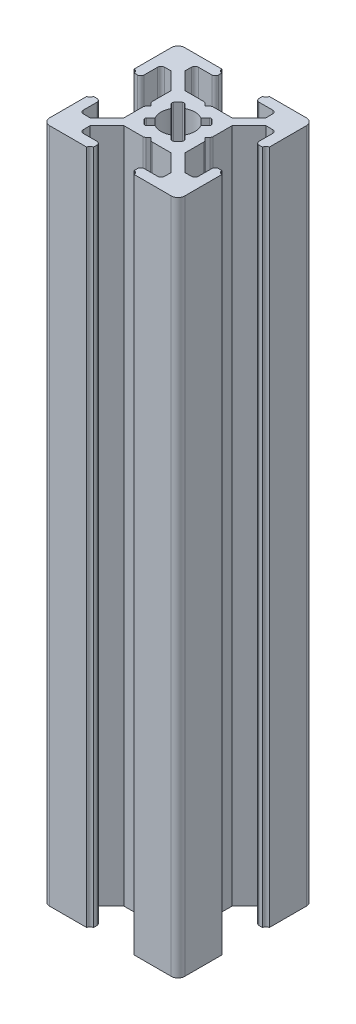
SolidWorks part; units mm, degrees
ref_plane "Front Plane" through (0, 0, 0) normal (0, 0, 1) x (1, 0, 0)
ref_plane "Top Plane" through (0, 0, 0) normal (0, 1, 0) x (1, 0, 0)
ref_plane "Right Plane" through (0, 0, 0) normal (1, 0, 0) x (0, 0, -1)
sketch "Sketch3" plane through (0, 0, 0) normal (0, 1, 0) x (1, 0, 0)
  line L0 (7, 20) -> (7, 18.5)
  line L1 (0, 0) -> (20, 0)
  line L2 (0, 0) -> (0, 20)
  line L3 (0, 20) -> (20, 20)
  line L4 (20, 0) -> (20, 20)
  line L5 (7, 18.5) -> (4, 18.5)
  line L6 (4, 18.5) -> (4, 17)
  line L7 (4, 17) -> (6.5, 14.5)
  line L8 (6.5, 14.5) -> (13.5, 14.5)
  line L9 (13.5, 14.5) -> (16, 17)
  line L10 (16, 17) -> (16, 18.5)
  line L11 (16, 18.5) -> (13, 18.5)
  line L12 (13, 18.5) -> (13, 20)
  line L13 (13, 20) -> (7, 20)
  line L14 (9.5, 14.5) -> (10, 14)
  line L15 (10, 14) -> (10.5, 14.5)
  line L16 (10.5, 14.5) -> (9.5, 14.5)
  line L17 (13, 19.5) -> (13, 20)
  line L18 (13.5, 20) -> (13, 20)
  line L19 (7, 19.5) -> (7, 20)
  line L20 (6.5, 20) -> (7, 20)
  line L21 (0, 13) -> (1.5, 13)
  line L22 (1.5, 13) -> (1.5, 16)
  line L23 (1.5, 16) -> (3, 16)
  line L24 (3, 16) -> (5.5, 13.5)
  line L25 (5.5, 13.5) -> (5.5, 6.5)
  line L26 (5.5, 6.5) -> (3, 4)
  line L27 (3, 4) -> (1.5, 4)
  line L28 (1.5, 4) -> (1.5, 7)
  line L29 (1.5, 7) -> (0, 7)
  line L30 (0, 7) -> (0, 13)
  line L31 (5.5, 10.5) -> (5.5, 9.5)
  line L32 (5.5, 9.5) -> (6, 10)
  line L33 (6, 10) -> (5.5, 10.5)
  line L34 (0.5, 13) -> (0, 13)
  line L35 (0, 13.5) -> (0, 13)
  line L36 (0, 6.5) -> (0, 7)
  line L37 (0.5, 7) -> (0, 7)
  line L38 (10, 20) -> (10, 0) construction
  line L39 (20, 10) -> (0, 10) construction
  line L40 (10, 6) -> (10.5, 5.5)
  line L41 (9.5, 5.5) -> (10, 6)
  line L42 (10.5, 5.5) -> (9.5, 5.5)
  line L43 (13.5, 0) -> (13, 0)
  line L44 (13, 0.5) -> (13, 0)
  line L45 (6.5, 0) -> (7, 0)
  line L46 (7, 0.5) -> (7, 0)
  line L47 (13, 1.5) -> (13, 0)
  line L48 (16, 1.5) -> (13, 1.5)
  line L49 (16, 3) -> (16, 1.5)
  line L50 (13.5, 5.5) -> (16, 3)
  line L51 (6.5, 5.5) -> (13.5, 5.5)
  line L52 (4, 3) -> (6.5, 5.5)
  line L53 (4, 1.5) -> (4, 3)
  line L54 (7, 1.5) -> (4, 1.5)
  line L55 (7, 0) -> (7, 1.5)
  line L56 (13, 0) -> (7, 0)
  line L57 (14.5, 9.5) -> (14, 10)
  line L58 (14.5, 10.5) -> (14.5, 9.5)
  line L59 (14, 10) -> (14.5, 10.5)
  line L60 (19.5, 7) -> (20, 7)
  line L61 (20, 6.5) -> (20, 7)
  line L62 (20, 13.5) -> (20, 13)
  line L63 (19.5, 13) -> (20, 13)
  line L64 (18.5, 7) -> (20, 7)
  line L65 (18.5, 4) -> (18.5, 7)
  line L66 (17, 4) -> (18.5, 4)
  line L67 (14.5, 6.5) -> (17, 4)
  line L68 (14.5, 13.5) -> (14.5, 6.5)
  line L69 (17, 16) -> (14.5, 13.5)
  line L70 (18.5, 16) -> (17, 16)
  line L71 (18.5, 13) -> (18.5, 16)
  line L72 (20, 13) -> (18.5, 13)
  line L73 (20, 7) -> (20, 13)
  arc A0 (13.5, 20) -> (13, 19.5) centre (13, 20) cw
  arc A1 (6.5, 20) -> (7, 19.5) centre (7, 20) ccw
  arc A2 (0.5, 13) -> (0, 13.5) centre (0, 13) ccw
  arc A3 (0.5, 7) -> (0, 6.5) centre (0, 7) cw
  arc A4 (13.5, 0) -> (13, 0.5) centre (13, 0) ccw
  arc A5 (6.5, 0) -> (7, 0.5) centre (7, 0) cw
  arc A6 (19.5, 7) -> (20, 6.5) centre (20, 7) ccw
  arc A7 (19.5, 13) -> (20, 13.5) centre (20, 13) cw
  point P7 (10, 14.5)
  point P16 (10, 20)
  point P26 (5.5, 10)
  point P35 (0, 10)
  dimension "D16" = 0.5
  dimension "D17" = 0.5
  dimension "D28" = 0.5
  dimension "D29" = 0.5
  dimension "D1" = 20
  dimension "D2" = 20
  dimension "D3" = 7
  dimension "D4" = 7
  dimension "D5" = 1.5
  dimension "D6" = 1.5
  dimension "D7" = 3
  dimension "D8" = 3
  dimension "D9" = 1.5
  dimension "D10" = 1.5
  dimension "D11" = 7
  dimension "D12" = 5.5
  dimension "D13" = 0.5
  dimension "D14" = 0.5
  dimension "D15" = 0.5
  dimension "D18" = 7
  dimension "D19" = 7
  dimension "D20" = 1.5
  dimension "D21" = 1.5
  dimension "D22" = 3
  dimension "D23" = 7
  dimension "D24" = 5.5
  dimension "D25" = 0.5
  dimension "D26" = 0.5
  dimension "D27" = 0.5
extrude "Boss-Extrude1" add sketch "Sketch3" along normal blind 100 contours L72 A7 L4 L3 A0 L12 L11 L10 L9 L8 L15 L14 L7 L6 L5 L0 A1 L2 A2 L21 L22 L23 L24 L25 L33 L32 L26 L27 L28 L29 A3 L1 A5 L55 L54 L53 L52 L51 L41 L40 L50 L49 L48 L47 A4
fillet "Fillet1" radius 1 4 edges at (0, 50, 0) (20, 50, 0) (20, 50, -20) (0, 50, -20)
sketch "Sketch4" plane through (0, 100, 0) normal (0, 1, 0) x (1, 0, 0)
  line L0 (13.5, 14.5) -> (5.5, 6.5) construction
  line L1 (14.5, 13.5) -> (6.5, 5.5) construction
  line L2 (10.5, 14.5) -> (14.5, 10.5) construction
  line L3 (12, 13) -> (13, 12)
  line L4 (13, 12) -> (8, 7)
  line L5 (8, 7) -> (7, 8)
  line L6 (7, 8) -> (12, 13)
  line L7 (13.5, 14.5) -> (16, 17) construction
  line L8 (17, 16) -> (14.5, 13.5) construction
  line L9 (5.5, 9.5) -> (9.5, 5.5) construction
  line L10 (5.5, 10.5) -> (9.5, 14.5) construction
  line L11 (14.5, 9.5) -> (10.5, 5.5) construction
  line L12 (6.5, 14.5) -> (14.5, 6.5) construction
  line L13 (5.5, 13.5) -> (13.5, 5.5) construction
  line L14 (7, 12) -> (8, 13)
  line L15 (8, 13) -> (13, 8)
  line L16 (13, 8) -> (12, 7)
  line L17 (12, 7) -> (7, 12)
  line L18 (4, 17) -> (6.5, 14.5) construction
  line L19 (3, 16) -> (5.5, 13.5) construction
  line L20 (20, 10) -> (0, 10) construction
  circle A0 centre (10, 10) radius 2.5
  dimension "D1" = 5
extrude "Cut-Extrude1" cut sketch "Sketch4" against normal through all contours L6 A0 L15 | L4 A0 L6 L15 | L15 A0 L17 L6 | L17 L4 L15 L6 | L17 A0 L6 | L6 A0 L4 L17 | L4 A0 L17 | L17 A0 L15 L4 | L15 A0 L4 | A0 L6 L5 L4 | A0 L17 L16 L15 | A0 L4 L3 L6 | A0 L15 L14 L17
fillet "Fillet2" radius 0.5 24 edges at (1.5, 50, -16) (1.5, 50, -13) (5.5, 50, -10.5) (5.5, 50, -9.5) (1.5, 50, -7) (1.5, 50, -4) (4, 50, -1.5) (7, 50, -1.5) (9.5, 50, -5.5) (10.5, 50, -5.5) (13, 50, -1.5) (16, 50, -1.5) (18.5, 50, -4) (18.5, 50, -7) (18.5, 50, -13) (18.5, 50, -16) (14.5, 50, -9.5) (14.5, 50, -10.5) (10.5, 50, -14.5) (9.5, 50, -14.5) (16, 50, -18.5) (13, 50, -18.5) (7, 50, -18.5) (4, 50, -18.5)
fillet "Fillet3" radius 0.25 8 edges at (13, 50, -8) (12, 50, -7) (13, 50, -12) (12, 50, -13) (8, 50, -13) (7, 50, -12) (7, 50, -8) (8, 50, -7)
